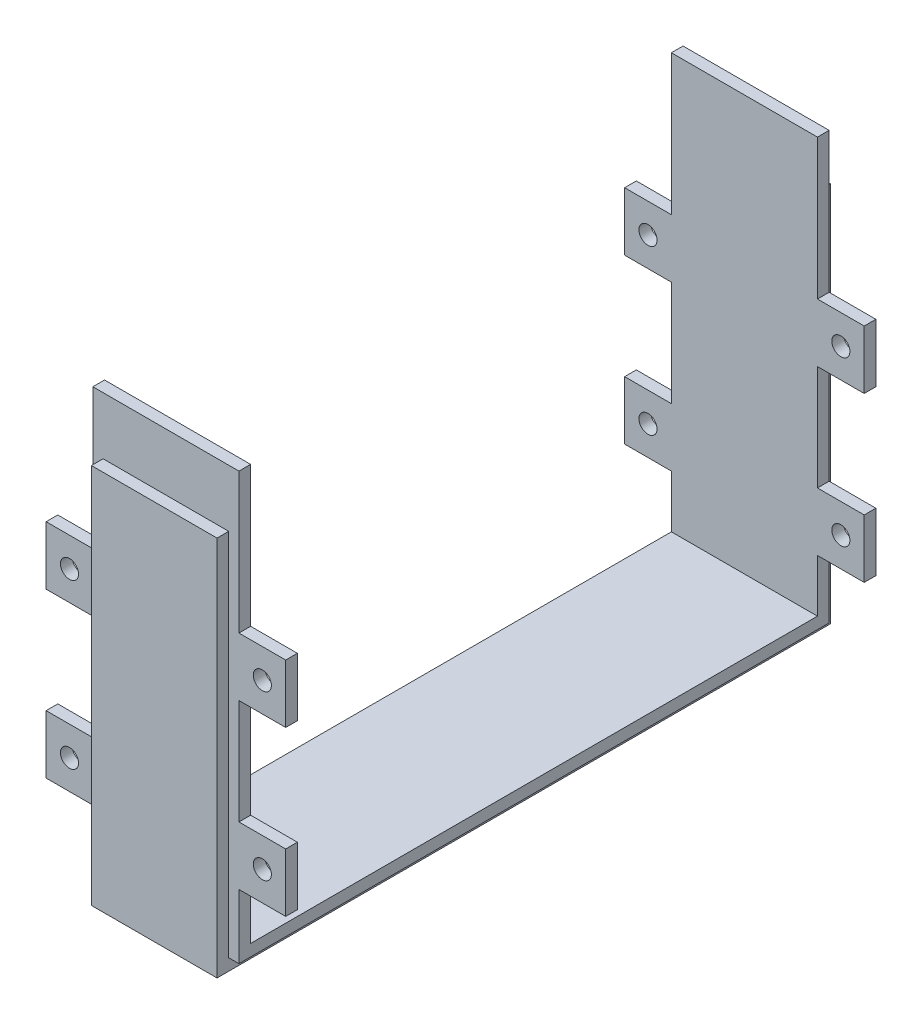
SolidWorks part; units mm, degrees
ref_plane "Front Plane" through (0, 0, 0) normal (0, 0, 1) x (1, 0, 0)
ref_plane "Top Plane" through (0, 0, 0) normal (0, 1, 0) x (1, 0, 0)
ref_plane "Right Plane" through (0, 0, 0) normal (1, 0, 0) x (0, 0, -1)
sketch "Sketch1" plane through (0, 0, 0) normal (1, 0, 0) x (0, 0, -1)
  line L1 (-52.5, 2) -> (52.5, 2)
  line L2 (-52.5, 2) -> (-52.5, -2)
  line L3 (-52.5, -2) -> (52.5, -2)
  line L4 (52.5, 2) -> (52.5, -2)
  line L5 (-52.5, 2) -> (52.5, -2) construction
  line L6 (-52.5, -2) -> (52.5, 2) construction
  line L7 (-52.5, 2) -> (-48.5, 2)
  line L8 (-52.5, 2) -> (-52.5, 63.2)
  line L9 (-52.5, 63.2) -> (-48.5, 63.2)
  line L10 (-48.5, 2) -> (-48.5, 63.2)
  line L11 (-48.5, 63.2) -> (-50.5, 63.2)
  line L12 (-48.5, 63.2) -> (-48.5, 73)
  line L13 (-48.5, 73) -> (-50.5, 73)
  line L14 (-50.5, 63.2) -> (-50.5, 73)
  line L15 (52.5, 2) -> (48.5, 2)
  line L16 (52.5, 2) -> (52.5, 63.2)
  line L17 (52.5, 63.2) -> (48.5, 63.2)
  line L18 (48.5, 2) -> (48.5, 63.2)
  line L19 (48.5, 63.2) -> (50.5, 63.2)
  line L20 (48.5, 63.2) -> (48.5, 73)
  line L21 (48.5, 73) -> (50.5, 73)
  line L22 (50.5, 63.2) -> (50.5, 73)
  point P0 (0, 0)
  dimension "D1" = 105
  dimension "D2" = 4
  dimension "D3" = 4
  dimension "D4" = 61.2
  dimension "D5" = 9.8
  dimension "D6" = 2
  dimension "D7" = 4
  dimension "D8" = 61.2
  dimension "D9" = 2
  dimension "D10" = 9.8
extrude "Boss-Extrude1" add sketch "Sketch1" along normal mid plane 25 contours L4 L1 L2 L3 | L1 L10 L9 L8 | L18 L1 L16 L17 | L12 L11 L14 L13 | L20 L19 L22 L21
sketch "Sketch2" plane through (0, 0, -48.5) normal (0, 0, 1) x (1, 0, 0)
  line L0 (-12.5, 2) -> (-12.5, 73) construction
  line L1 (-12.5, 11) -> (-20.5, 11)
  line L2 (-12.5, 11) -> (-12.5, 21)
  line L3 (-12.5, 21) -> (-20.5, 21)
  line L4 (-20.5, 11) -> (-20.5, 21)
  line L5 (12.5, 2) -> (-12.5, 2) construction
  line L6 (0, 73) -> (0, 13.7024) construction
  line L7 (-12.5, 39) -> (-20.5, 39)
  line L8 (-12.5, 39) -> (-12.5, 49)
  line L9 (-12.5, 49) -> (-20.5, 49)
  line L10 (-20.5, 39) -> (-20.5, 49)
  line L11 (12.5, 73) -> (-12.5, 73) construction
  line L12 (12.5, 21) -> (20.5, 21)
  line L13 (20.5, 11) -> (20.5, 21)
  line L14 (12.5, 11) -> (20.5, 11)
  line L15 (12.5, 11) -> (12.5, 21)
  line L16 (12.5, 49) -> (20.5, 49)
  line L17 (20.5, 39) -> (20.5, 49)
  line L18 (12.5, 39) -> (20.5, 39)
  line L19 (12.5, 39) -> (12.5, 49)
  circle A0 centre (-16.5, 44) radius 1.55
  circle A1 centre (-16.5, 16) radius 1.55
  circle A2 centre (16.5, 16) radius 1.55
  circle A3 centre (16.5, 44) radius 1.55
  dimension "D7" = 3.1
  dimension "D8" = 3.1
  dimension "D1" = 10
  dimension "D2" = 8
  dimension "D3" = 9
  dimension "D4" = 10
  dimension "D5" = 8
  dimension "D6" = 18
extrude "Boss-Extrude2" add sketch "Sketch2" against normal blind 2
sketch "Sketch4" plane through (0, 0, 48.5) normal (0, 0, -1) x (-1, 0, 0)
  line L0 (-12.5, 2) -> (-12.5, 73) construction
  line L1 (-12.5, 11) -> (-20.5, 11)
  line L2 (-12.5, 11) -> (-12.5, 21)
  line L3 (-12.5, 21) -> (-20.5, 21)
  line L4 (-20.5, 11) -> (-20.5, 21)
  line L5 (-12.5, 2) -> (12.5, 2) construction
  line L6 (0, 73) -> (0, 7.87) construction
  line L7 (-12.5, 39) -> (-20.5, 39)
  line L8 (-12.5, 39) -> (-12.5, 49)
  line L9 (-12.5, 49) -> (-20.5, 49)
  line L10 (-20.5, 39) -> (-20.5, 49)
  line L11 (-12.5, 73) -> (12.5, 73) construction
  line L12 (12.5, 21) -> (20.5, 21)
  line L13 (20.5, 11) -> (20.5, 21)
  line L14 (12.5, 11) -> (20.5, 11)
  line L15 (12.5, 11) -> (12.5, 21)
  line L16 (12.5, 49) -> (20.5, 49)
  line L17 (20.5, 39) -> (20.5, 49)
  line L18 (12.5, 39) -> (20.5, 39)
  line L19 (12.5, 39) -> (12.5, 49)
  circle A0 centre (-16.5, 44) radius 1.55
  circle A1 centre (-16.5, 16) radius 1.55
  circle A2 centre (16.5, 16) radius 1.55
  circle A3 centre (16.5, 44) radius 1.55
  dimension "D7" = 3.1
  dimension "D8" = 3.1
  dimension "D1" = 8
  dimension "D2" = 10
  dimension "D3" = 9
  dimension "D4" = 8
  dimension "D5" = 10
  dimension "D6" = 18
extrude "Boss-Extrude3" add sketch "Sketch4" against normal blind 2
sketch "Sketch5" plane through (-12.5, 0, 0) normal (-1, 0, 0) x (0, 0, 1)
  line L0 (52.5, -2) -> (-52.5, -2) construction
  line L1 (-52.5, 63.2) -> (-50.5, 63.2)
  line L2 (-52.5, 63.2) -> (-52.5, -2)
  line L3 (-52.5, -2) -> (-50.5, -2)
  line L4 (-50.5, 63.2) -> (-50.5, -2)
  line L6 (52.5, 63.2) -> (50.5, 63.2)
  line L7 (52.5, 63.2) -> (52.5, -2)
  line L8 (52.5, -2) -> (50.5, -2)
  line L9 (50.5, 63.2) -> (50.5, -2)
  line L10 (-50.5, -2) -> (50.5, -2)
  line L11 (-50.5, -2) -> (-50.5, 0)
  line L12 (-50.5, 0) -> (50.5, 0)
  line L13 (50.5, -2) -> (50.5, 0)
  line M7 (50.5, 49) -> (50.5, 39)
  line M11 (50.5, 21) -> (50.5, 11)
  line M17 (-50.5, 11) -> (-50.5, 21)
  line M21 (-50.5, 39) -> (-50.5, 49)
  line M26 (-50.5, 63.2) -> (-52.5, 63.2)
  line M27 (-52.5, 63.2) -> (-52.5, -2)
  line M28 (-52.5, -2) -> (52.5, -2)
  line M29 (52.5, -2) -> (52.5, 63.2)
  line M30 (52.5, 63.2) -> (50.5, 63.2)
  dimension "D1" = 2
  dimension "D2" = 2
  dimension "D3" = 2
extrude "Cut-Extrude1" cut sketch "Sketch5" against normal blind 1.75 contours L4 M26 M27 M28 M17 M21 | L12 L4 L9 M28 | L9 M30 M7 M11 M28 M29
sketch "Sketch6" plane through (12.5, 0, 0) normal (1, 0, 0) x (0, 0, -1)
  line L1 (-50.5, 63.2) -> (-52.5, 63.2)
  line L2 (-50.5, 63.2) -> (-50.5, -2)
  line L3 (-50.5, -2) -> (-52.5, -2)
  line L4 (-52.5, 63.2) -> (-52.5, -2)
  line L5 (50.5, 63.2) -> (52.5, 63.2)
  line L6 (50.5, 63.2) -> (50.5, -2)
  line L7 (50.5, -2) -> (52.5, -2)
  line L8 (52.5, 63.2) -> (52.5, -2)
  line L9 (-50.5, -2) -> (50.5, -2)
  line L10 (-50.5, -2) -> (-50.5, 0)
  line L11 (-50.5, 0) -> (50.5, 0)
  line L12 (50.5, -2) -> (50.5, 0)
  line M15 (-52.5, -2) -> (52.5, -2)
  dimension "D1" = 2
extrude "Cut-Extrude2" cut sketch "Sketch6" against normal blind 1.75 contours L11 L2 L6 M15
